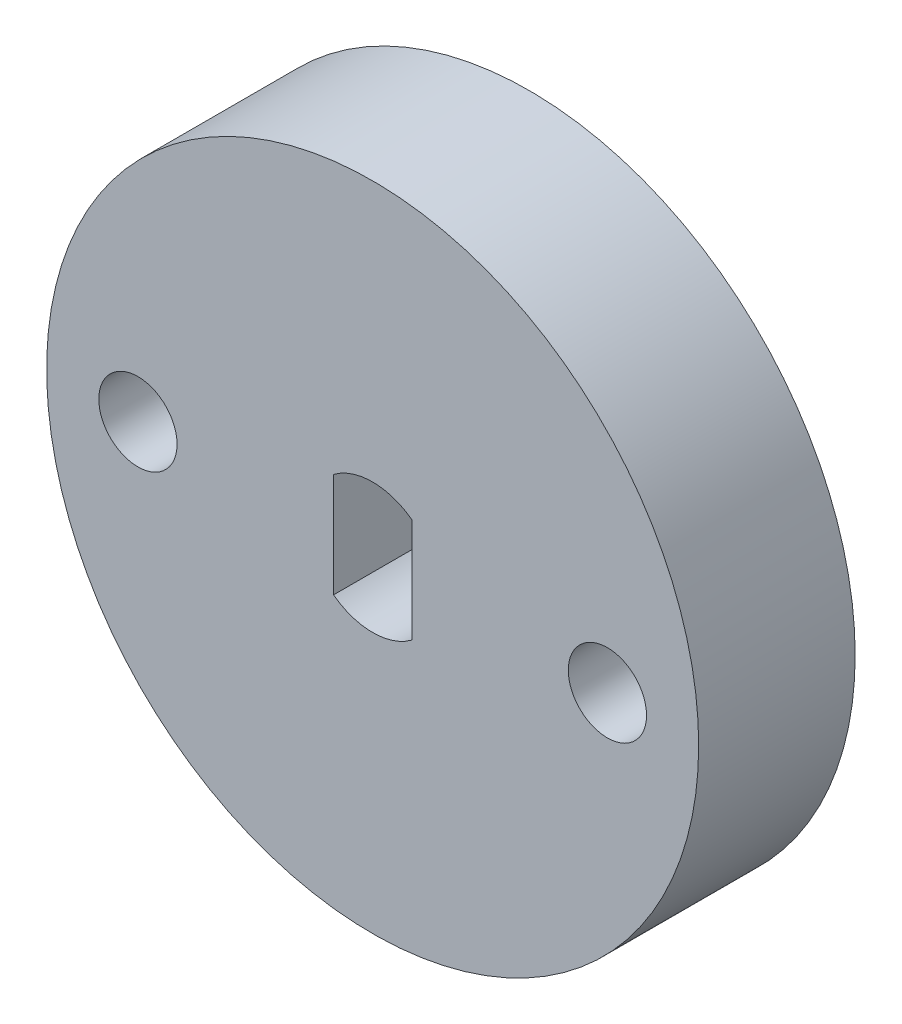
SolidWorks part; units mm, degrees
ref_plane "Front Plane" through (0, 0, 0) normal (0, 0, 1) x (1, 0, 0)
ref_plane "Top Plane" through (0, 0, 0) normal (0, 1, 0) x (1, 0, 0)
ref_plane "Right Plane" through (0, 0, 0) normal (1, 0, 0) x (0, 0, -1)
sketch "Sketch1" plane through (0, 0, 0) normal (0, 0, 1) x (1, 0, 0)
  line L0 (-12.5, 0) -> (12.5, 0) construction
  line L1 (-1.5, 2) -> (-1.5, -2)
  line L2 (1.5, 2) -> (1.5, -2)
  circle A0 centre (0, 0) radius 12.5
  circle A1 centre (-9, 0) radius 1.5
  circle A2 centre (9, 0) radius 1.5
  circle A3 centre (0, 0) radius 2.5
  dimension "D1" = 25
  dimension "D3" = 3
  dimension "D5" = 3
  dimension "D6" = 5
  dimension "D7" = 3.5
  dimension "D2" = 9
  dimension "D4" = 9
  dimension "D8" = 3.5
  dimension "D9" = 1.5
  dimension "D10" = 1.5
extrude "Boss-Extrude1" add sketch "Sketch1" along normal blind 6 contours L0 A0 A2 A3 A1 | A0 L0 A1 A3 A2 | L0 A3 L1 | A3 L0 L1 | L2 L0 A3 | L0 L2 A3
